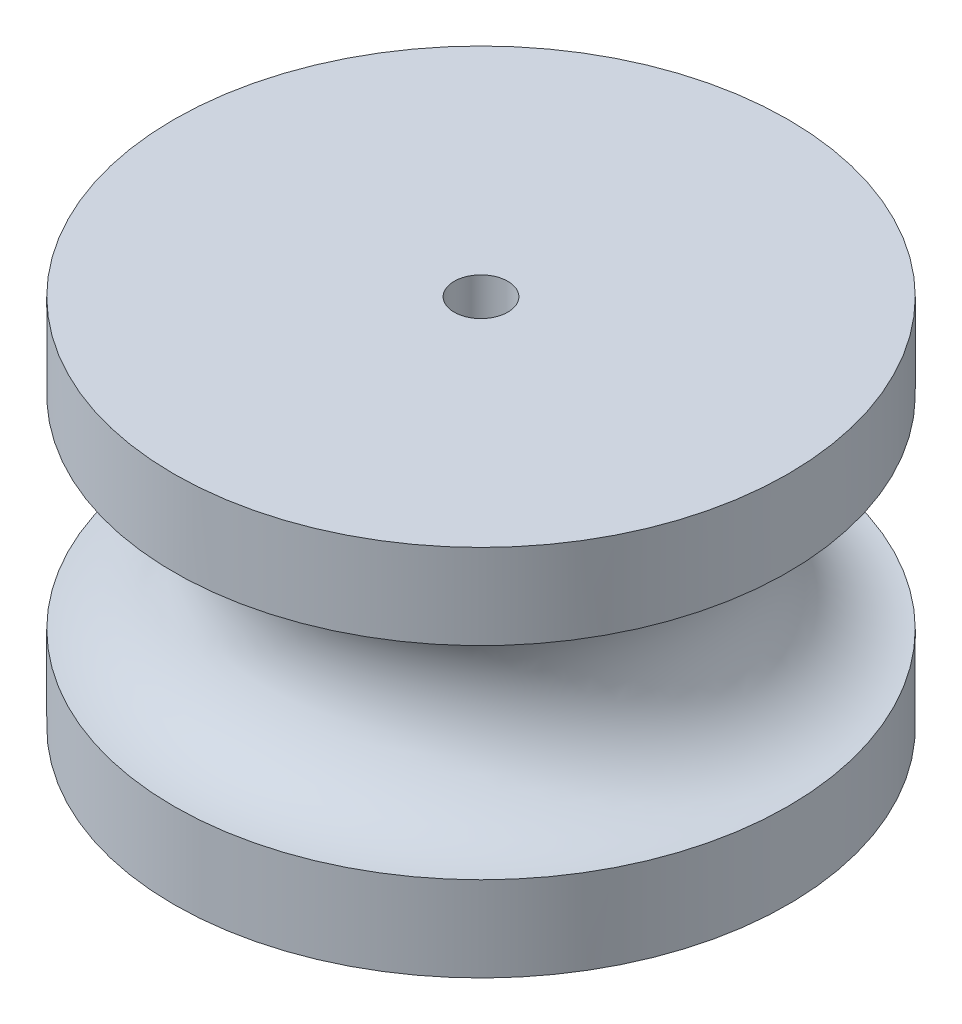
SolidWorks part; units mm, degrees
ref_plane "Front Plane" through (0, 0, 0) normal (0, 0, 1) x (1, 0, 0)
ref_plane "Top Plane" through (0, 0, 0) normal (0, 1, 0) x (1, 0, 0)
ref_plane "Right Plane" through (0, 0, 0) normal (1, 0, 0) x (0, 0, -1)
sketch "Sketch1" plane through (0, 0, 0) normal (0, 1, 0) x (1, 0, 0)
  line L2 (-1.88, 1.9379) -> (-1.88, -1.9379)
  line L4 (1.88, 1.9379) -> (1.88, -1.9379)
  arc A0 (-1.88, -1.9379) -> (1.88, -1.9379) centre (0, 0) ccw
  arc A1 (1.88, 1.9379) -> (-1.88, 1.9379) centre (0, 0) ccw
  circle A2 centre (0, 0) radius 7
  point P0 (0, 0)
  dimension "D2" = 5.4
  dimension "D1" = 14
extrude "Boss-Extrude1" add sketch "Sketch1" along normal blind 6.5
sketch "Sketch2" plane through (0, 6.5, 0) normal (0, 1, 0) x (1, 0, 0)
  circle A0 centre (0, 0) radius 0.6112
  circle A1 centre (0, 0) radius 7
  circle A2 centre (0, 0) radius 7 construction
extrude "Boss-Extrude2" add sketch "Sketch2" along normal blind 2
sketch "Sketch3" plane through (0, 0, 0) normal (1, 0, 0) x (0, 0, -1)
  line L0 (-7, 8.5) -> (-7, 0) construction
  line L1 (0, 0) -> (0, 12.4161) construction
  circle A0 centre (-7, 4.25) radius 2.311
revolve "Cut-Revolve1" cut sketch "Sketch3" angle 360 about L1
